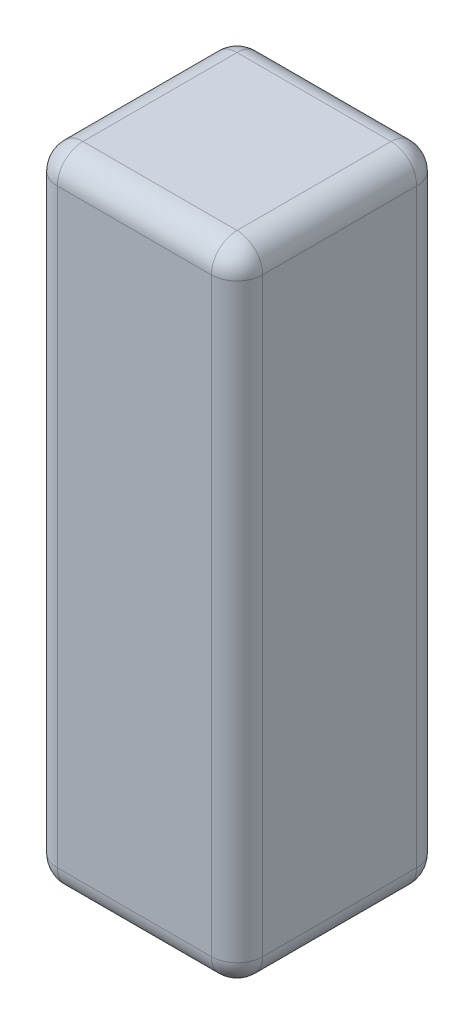
SolidWorks part; units mm, degrees
ref_plane "Front Plane" through (0, 0, 0) normal (0, 0, 1) x (1, 0, 0)
ref_plane "Top Plane" through (0, 0, 0) normal (0, 1, 0) x (1, 0, 0)
ref_plane "Right Plane" through (0, 0, 0) normal (1, 0, 0) x (0, 0, -1)
sketch "Sketch1" plane through (0, 0, 0) normal (0, 0, 1) x (1, 0, 0)
  line L1 (52.5859, -113.7766) -> (84.5859, -113.7766)
  line L2 (52.5859, -113.7766) -> (52.5859, -213.7766)
  line L3 (52.5859, -213.7766) -> (84.5859, -213.7766)
  line L4 (84.5859, -113.7766) -> (84.5859, -213.7766)
  dimension "D1" = 32
  dimension "D2" = 100
extrude "Boss-Extrude1" add sketch "Sketch1" against normal blind 32
fillet "Fillet1" radius 4 12 edges at (52.5859, -213.7766, -16) (84.5859, -213.7766, -16) (68.5859, -213.7766, 0) (52.5859, -163.7766, 0) (84.5859, -163.7766, 0) (52.5859, -163.7766, -32) (52.5859, -113.7766, -16) (68.5859, -113.7766, 0) (84.5859, -113.7766, -16) (68.5859, -113.7766, -32) (84.5859, -163.7766, -32) (68.5859, -213.7766, -32)
